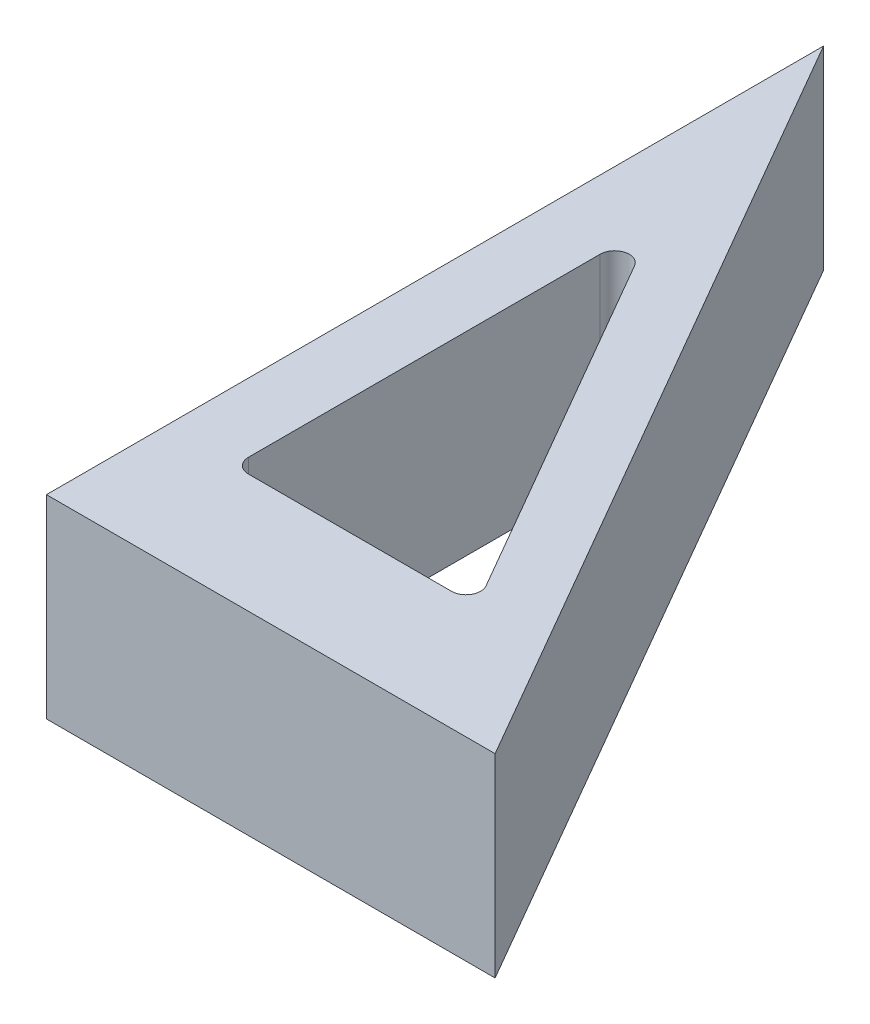
SolidWorks part; units mm, degrees
ref_plane "Front Plane" through (0, 0, 0) normal (0, 0, 1) x (1, 0, 0)
ref_plane "Top Plane" through (0, 0, 0) normal (0, 1, 0) x (1, 0, 0)
ref_plane "Right Plane" through (0, 0, 0) normal (1, 0, 0) x (0, 0, -1)
sketch "Sketch1" plane through (0, 0, 0) normal (0, 1, 0) x (1, 0, 0)
  line L0 (0, 0) -> (0, 80)
  line L1 (0, 80) -> (46.188, 0)
  line L2 (46.188, 0) -> (0, 0)
  dimension "D1" = 80
  dimension "D2" = 60
extrude "Boss-Extrude1" add sketch "Sketch1" along normal blind 20
sketch "Sketch2" plane through (0, 20, 0) normal (0, 1, 0) x (1, 0, 0)
  line L0 (7.0627, 55.5342) -> (7.0627, 12.2329)
  line L1 (7.0627, 12.2329) -> (32.0627, 12.2329)
  line L2 (32.0627, 12.2329) -> (7.0627, 55.5342)
  line L3 (0, 80) -> (0, 0) construction
  line L4 (7.0627, 12.2329) -> (0, 12.2329) construction
  line L5 (32.0627, 12.2329) -> (39.1253, 12.2329) construction
  line L6 (46.188, 0) -> (0, 80) construction
  line L7 (7.0627, 55.5342) -> (7.0627, 67.7671) construction
  line L8 (7.0627, 12.2329) -> (7.0627, 0) construction
  line L9 (0, 0) -> (46.188, 0) construction
  dimension "D1" = 25
extrude "Cut-Extrude1" cut sketch "Sketch2" against normal through all
fillet "Fillet1" radius 1.5 3 edges at (32.0627, 10, -12.2329) (7.0627, 10, -12.2329) (7.0627, 10, -55.5342)
